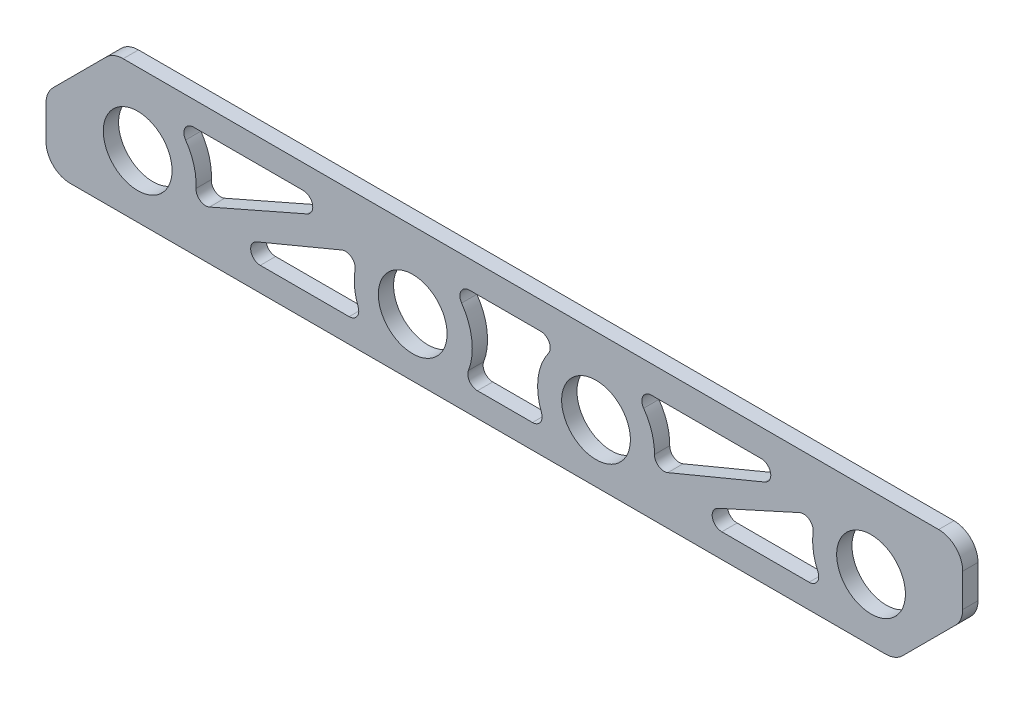
SolidWorks part; units mm, degrees
ref_plane "Front Plane" through (0, 0, 0) normal (0, 0, 1) x (1, 0, 0)
ref_plane "Top Plane" through (0, 0, 0) normal (0, 1, 0) x (1, 0, 0)
ref_plane "Right Plane" through (0, 0, 0) normal (1, 0, 0) x (0, 0, -1)
sketch "Sketch1" plane through (0, 0, 0) normal (0, 0, 1) x (1, 0, 0)
  line L0 (190.5, 44.5456) -> (190.5, 0) construction
  line L1 (0, 0) -> (381, 0)
  line L2 (0, 0) -> (0, 27.94)
  line L3 (0, 55.88) -> (381, 55.88)
  line L4 (381, 27.94) -> (381, 55.88)
  line L5 (0, 27.94) -> (27.94, 55.88)
  line L6 (381, 27.94) -> (353.06, 0)
  line L9 (69.0594, 10) -> (132.6459, 10)
  line L10 (51.6409, 45.88) -> (125.9405, 45.88)
  line L13 (172.737, 10) -> (208.8459, 10)
  line L14 (262.3779, 10) -> (324.384, 10)
  line L15 (166.4162, 44.5456) -> (215.4438, 44.5456)
  line L16 (10, 23.7979) -> (35.0111, 48.8089) construction
  line L17 (241.7562, 44.5456) -> (317.2574, 44.5456)
  line L21 (361.416, 10) -> (363.06, 10)
  line L22 (10, 10) -> (381, 10) construction
  line L23 (10, 10) -> (10, 23.7979) construction
  line L24 (262.3779, 10) -> (321.2405, 36.706)
  line L25 (69.0594, 10) -> (131.1338, 35.8617)
  line L26 (60.8964, 17.3384) -> (125.9405, 45.88)
  line L27 (251.9289, 17.3738) -> (317.2574, 44.5456)
  circle A0 centre (38.1, 25.7175) radius 14.2875
  circle A1 centre (152.4, 24.13) radius 14.2875
  circle A2 centre (228.6, 24.13) radius 14.2875
  circle A3 centre (342.9, 25.7175) radius 14.2875
  arc A4 (60.8964, 17.3384) -> (51.6409, 45.88) centre (38.1, 25.7175) ccw
  arc A5 (131.1338, 35.8617) -> (132.6459, 10) centre (152.4, 24.13) ccw
  arc A7 (241.7562, 44.5456) -> (251.9289, 17.3738) centre (228.6, 24.13) cw
  circle A8 centre (38.1, 25.7175) radius 24.2875 construction
  circle A9 centre (152.4, 24.13) radius 24.2875 construction
  circle A10 centre (228.6, 24.13) radius 24.2875 construction
  arc A11 (208.8459, 10) -> (215.4438, 44.5456) centre (228.6, 24.13) cw
  arc A12 (324.384, 10) -> (321.2405, 36.706) centre (342.9, 25.7175) cw
  arc A13 (172.737, 10) -> (166.4162, 44.5456) centre (152.4, 24.13) ccw
  dimension "D3" = 28.575
  dimension "D6" = 28.575
  dimension "D7" = 38.1
  dimension "D8" = 10
  dimension "D2" = 10
  dimension "D4" = 38.1
  dimension "D5" = 30.1625
  dimension "D9" = 10
  dimension "D10" = 10
extrude "Boss-Extrude1" add sketch "Sketch1" along normal blind 6.35
fillet "Fillet1" radius 10 6 edges at (353.06, 0, 3.175) (381, 27.94, 3.175) (27.94, 55.88, 3.175) (0, 27.94, 3.175) (0, 0, 3.175) (381, 55.88, 3.175)
fillet "Fillet2" radius 4 12 edges at (321.2405, 36.706, 3.175) (262.3779, 10, 3.175) (251.9289, 17.3738, 3.175) (317.2574, 44.5456, 3.175) (215.4438, 44.5456, 3.175) (172.737, 10, 3.175) (208.8459, 10, 3.175) (166.4162, 44.5456, 3.175) (131.1338, 35.8617, 3.175) (69.0594, 10, 3.175) (125.9405, 45.88, 3.175) (60.8964, 17.3384, 3.175)
fillet "Fillet3" radius 4 4 edges at (324.384, 10, 3.175) (241.7562, 44.5456, 3.175) (132.6459, 10, 3.175) (51.6409, 45.88, 3.175)
